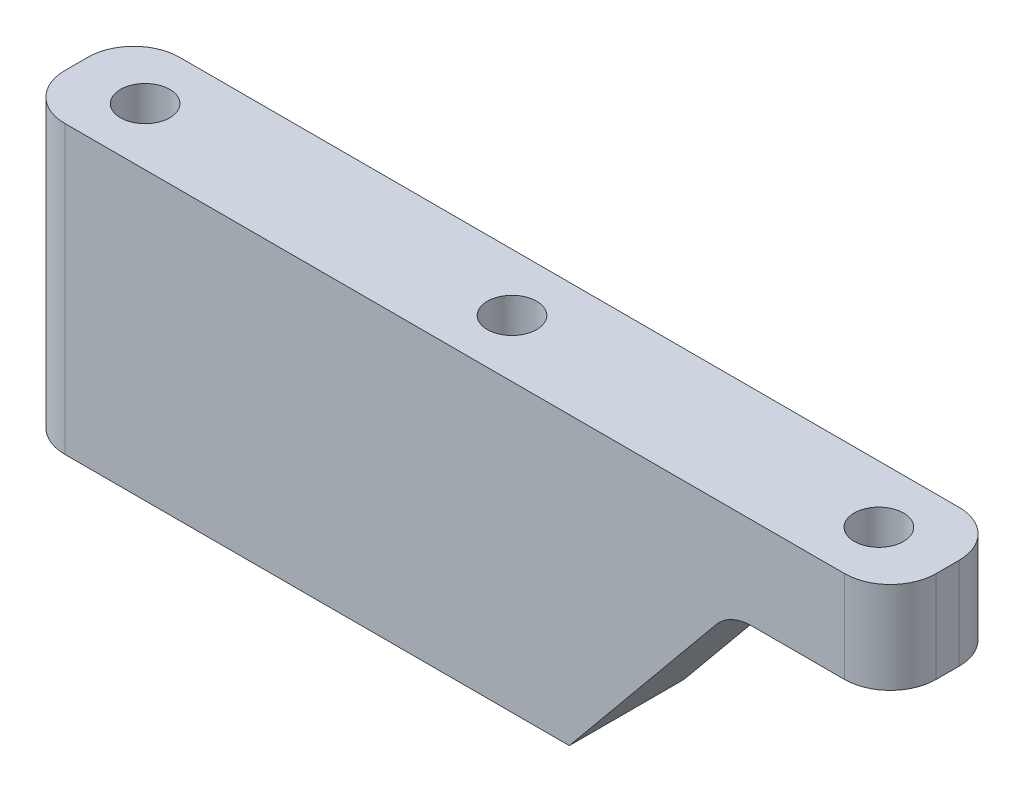
SolidWorks part; units mm, degrees
material "PE Low Density Film"
ref_plane "Front Plane" through (0, 0, 0) normal (0, 0, 1) x (1, 0, 0)
ref_plane "Top Plane" through (0, 0, 0) normal (0, 1, 0) x (1, 0, 0)
ref_plane "Right Plane" through (0, 0, 0) normal (1, 0, 0) x (0, 0, -1)
sketch "Sketch2" plane through (0, 0, 0) normal (0, 1, 0) x (1, 0, 0)
  line L0 (-32, 0) -> (32, 0) construction
  line L1 (-38, -5) -> (38, -5)
  line L2 (-38, -5) -> (-38, 5)
  line L3 (-38, 5) -> (38, 5)
  line L4 (38, -5) -> (38, 5)
  line L5 (-38, -5) -> (38, 5) construction
  line L6 (-38, 5) -> (38, -5) construction
  circle A0 centre (-32, 0) radius 2.15
  circle A1 centre (0, 0) radius 2.15
  circle A2 centre (32, 0) radius 2.15
  point P0 (0, 0)
  point P10 (0, 0)
  dimension "D4" = 4.3
  dimension "D1" = 76
  dimension "D2" = 10
  dimension "D3" = 32
extrude "Boss-Extrude1" add sketch "Sketch2" along normal blind 25
sketch "Sketch3" plane through (0, 0, 5) normal (0, 0, 1) x (1, 0, 0)
  line L0 (38, 17) -> (24, 17)
  line L1 (38, 25) -> (38, 0) construction
  line L2 (24, 17) -> (10, 0)
  line L3 (-38, 0) -> (38, 0) construction
  line L4 (10, 0) -> (38, 0)
  line L5 (38, 0) -> (38, 17)
  line L6 (-38, 25) -> (38, 25) construction
  point P13 (0, 0)
  dimension "D1" = 8
  dimension "D2" = 10
  dimension "D3" = 14
extrude "Cut-Extrude1" cut sketch "Sketch3" against normal blind 27
fillet "Fillet1" radius 4 5 edges at (-38, 12.5, -5) (-38, 12.5, 5) (38, 21, -5) (38, 21, 5) (24, 17, 0)
